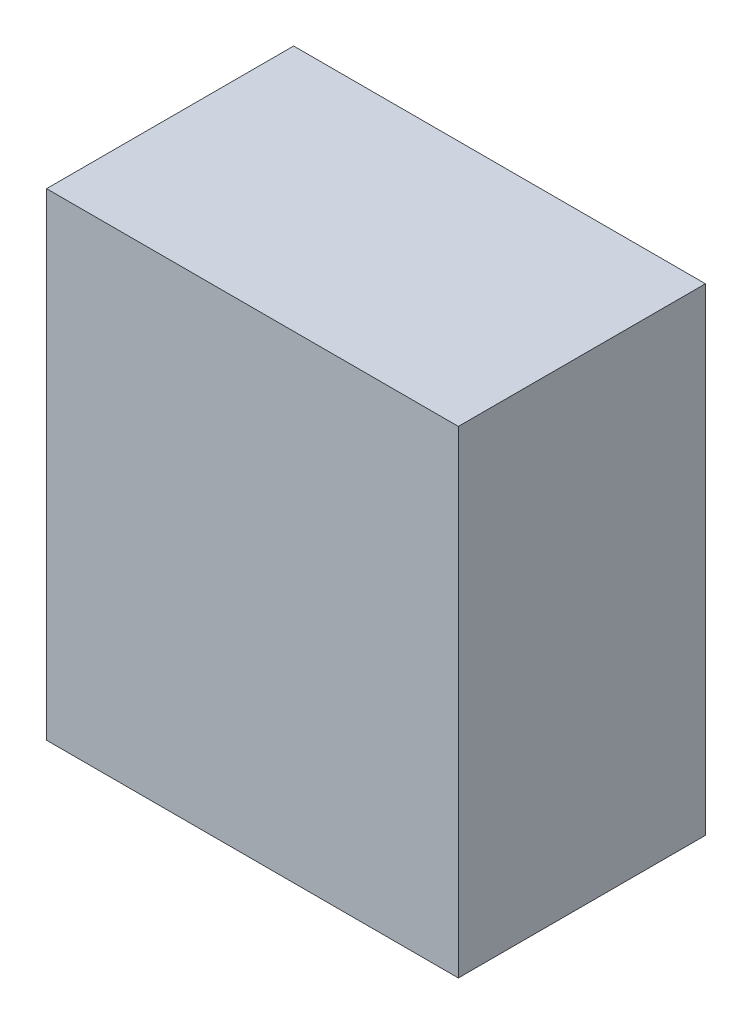
SolidWorks part; units mm, degrees
ref_plane "Front" through (0, 0, 0) normal (0, 0, 1) x (1, 0, 0)
ref_plane "Top" through (0, 0, 0) normal (0, 1, 0) x (1, 0, 0)
ref_plane "Right" through (0, 0, 0) normal (1, 0, 0) x (0, 0, -1)
sketch "Sketch1" plane through (0, 0, 0) normal (0, 1, 0) x (1, 0, 0)
  line L1 (-5, -3) -> (5, -3)
  line L2 (-5, -3) -> (-5, 3)
  line L3 (-5, 3) -> (5, 3)
  line L4 (5, -3) -> (5, 3)
  line L5 (-5, -3) -> (5, 3) construction
  line L6 (-5, 3) -> (5, -3) construction
  point P0 (0, 0)
  dimension "D1" = 6
  dimension "D2" = 10
extrude "Boss-Extrude1" add sketch "Sketch1" along normal blind 11.6
